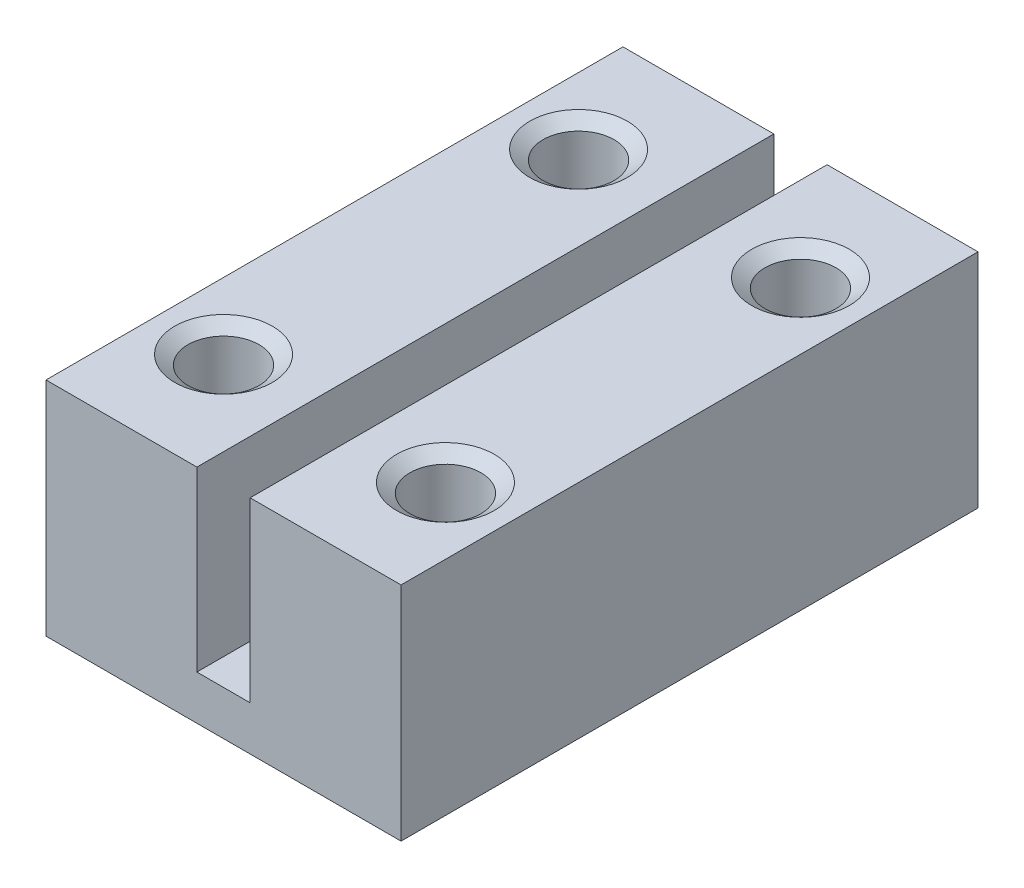
SolidWorks part; units mm, degrees
ref_plane "Спереди" through (0, 0, 0) normal (0, 0, 1) x (1, 0, 0)
ref_plane "Сверху" through (0, 0, 0) normal (0, 1, 0) x (1, 0, 0)
ref_plane "Справа" through (0, 0, 0) normal (1, 0, 0) x (0, 0, -1)
sketch "Эскиз1" plane through (0, 0, 0) normal (0, 0, 1) x (1, 0, 0)
  line L0 (-4, 5) -> (-0.6, 5)
  line L1 (-4, 0) -> (4, 0)
  line L2 (-4, 0) -> (-4, 5)
  line L3 (-0.6, 5) -> (-0.6, 1)
  line L4 (4, 0) -> (4, 5)
  line L5 (-0.6, 1) -> (0.6, 1)
  line L6 (0.6, 1) -> (0.6, 5)
  line L7 (0.6, 5) -> (4, 5)
  point P4 (0, 1)
  dimension "D1" = 8
  dimension "D2" = 1.2
  dimension "D3" = 4
  dimension "D4" = 5
extrude "Бобышка-Вытянуть1" add sketch "Эскиз1" along normal blind 13
hole_wizard "Отверстие обработанное метчиком M2x0.41" positions "Эскиз3" profile "Эскиз2" tap size "M2x0.4" standard "Ansi (метрические)" end condition up to next
sketch "Эскиз3" plane through (0, 0, 0) normal (0, -1, 0) x (1, 0, 0)
  line L0 (-4, 0) -> (4, 0) construction
  point P0 (-2.5, 10.5)
  point P1 (2.5, 10.5)
  point P3 (2.5, 2.5)
  point P5 (-2.5, 2.5)
  dimension "D1" = 2.5
  dimension "D2" = 5
  dimension "D3" = 8
  dimension "D4" = 2.5
sketch "Эскиз2" plane through (-2.5, 0, 10.5) normal (1, 0, 0) x (0, 0, -1)
  line L0 (0, 0) -> (0, 5)
  line L1 (0, 5) -> (1.1, 5)
  line L2 (0.8, 4.7899) -> (0.8, 0.3)
  line L3 (0.8, 0.3) -> (1.1, 0)
  line L5 (1.1, 0) -> (0, 0)
  line L6 (-0.8, 0.3) -> (-1.1, 0) construction
  line L7 (1.1, 5) -> (0.8, 4.7899)
  line L8 (-1.1, 5) -> (-0.8, 4.7899) construction
  line L11 (0, -6.35) -> (0, 107.95) construction
  dimension "Диаметр проходного сверла" = 1.6
  dimension "Глубина проходного сверла" = 5
  dimension "Диаметр передней зенковки" = 2.2
  dimension "Угол передней зенковки" = 90
  dimension "Диаметр задней зенковки" = 2.2
  dimension "Угол задней зенковки" = 110
cosmetic thread "Отверстие резьбы1"
cosmetic thread "Отверстие резьбы2"
cosmetic thread "Отверстие резьбы3"
cosmetic thread "Отверстие резьбы4"
